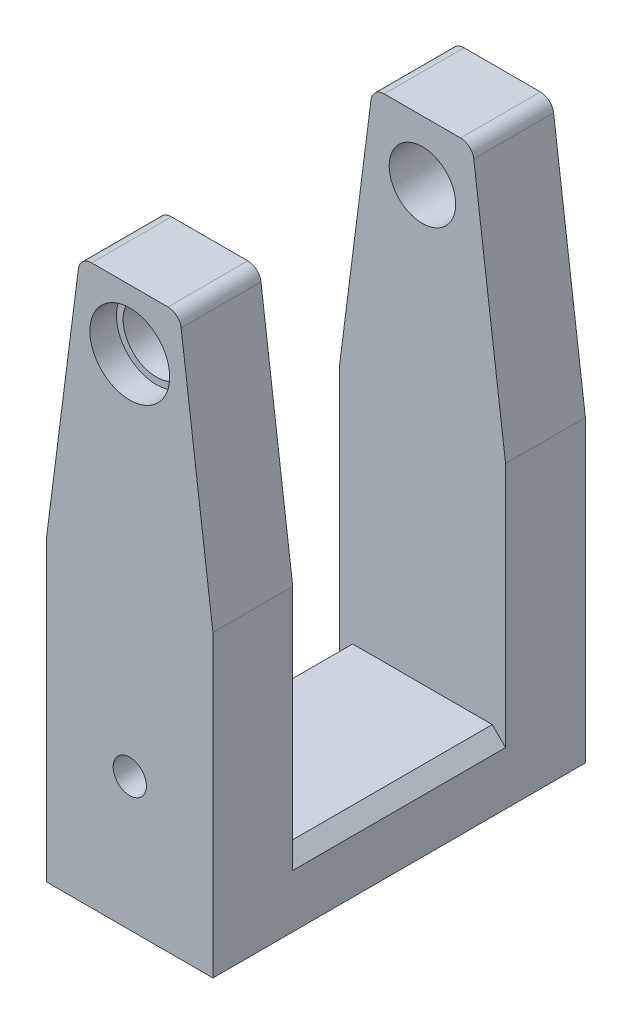
SolidWorks part; units mm, degrees
ref_plane "Front Plane" through (0, 0, 0) normal (0, 0, 1) x (1, 0, 0)
ref_plane "Top Plane" through (0, 0, 0) normal (0, 1, 0) x (1, 0, 0)
ref_plane "Right Plane" through (0, 0, 0) normal (1, 0, 0) x (0, 0, -1)
sketch "Sketch15" plane through (0, 0, 0) normal (0, 0, 1) x (1, 0, 0)
  line L6 (-12.5, 0) -> (12.5, 0)
  line L7 (0, 0) -> (0, 84) construction
  line L8 (-7.5, 84) -> (7.5, 84)
  line L9 (-12.5, 0) -> (-12.5, 45)
  line L10 (12.5, 0) -> (12.5, 45)
  line L11 (-12.5, 45) -> (-7.5, 84)
  line L12 (7.5, 84) -> (12.5, 45)
  point P4 (0, 0)
  point P9 (0, 84)
  dimension "D1" = 25
  dimension "D2" = 84
  dimension "D3" = 45
  dimension "D4" = 15
  dimension "D5" = 45
extrude "Boss-Extrude2" add sketch "Sketch15" along normal mid plane 56
sketch "Sketch16" plane through (12.5, 0, 0) normal (1, 0, 0) x (0, 0, -1)
  line L0 (-28, 84) -> (28, 84) construction
  line L1 (-16, 84) -> (16, 84)
  line L2 (-16, 84) -> (-16, 10)
  line L3 (-16, 10) -> (16, 10)
  line L4 (16, 84) -> (16, 10)
  line L5 (28, 45) -> (28, 84) construction
  line L6 (-28, 0) -> (28, 0) construction
  dimension "D1" = 12
  dimension "D2" = 32
  dimension "D3" = 10
extrude "Cut-Extrude3" cut sketch "Sketch16" against normal through all
hole_wizard "CBORE for M4 Hex Socket Head Cap Screw1" positions "Sketch17" profile "Sketch18" counterbore size "M4" standard "ISO"
sketch "Sketch17" plane through (0, 0, 28) normal (0, 0, 1) x (1, 0, 0)
  line L0 (0, 84) -> (0, 75) construction
  line L1 (7.5, 84) -> (-7.5, 84) construction
  point P0 (0, 75)
  dimension "D1" = 9
sketch "Sketch18" plane through (0, 75, 28) normal (1, 0, 0) x (0, -1, 0)
  line L0 (0, 0) -> (0, 23.0043)
  line L1 (0, 23.0043) -> (5, 20)
  line L2 (5, 20) -> (5, 4)
  line L3 (5, 4) -> (6, 4)
  line L4 (6, 4) -> (6, 0)
  line L5 (6, 0) -> (0, 0)
  line L10 (0, 23.0043) -> (-5, 20) construction
  line L11 (0, -6.35) -> (0, 107.95) construction
  dimension "Hole Dia." = 10
  dimension "Hole Depth" = 20
  dimension "C'Bore Dia." = 12
  dimension "C'Bore Depth" = 4
  dimension "Drill Angle" = 118
mirror "Mirror1" about plane through (0, 0, 0) normal (0, 0, 1) of "CBORE for M4 Hex Socket Head Cap Screw1"
hole_wizard "M6 Tapped Hole1" positions "Sketch19" profile "Sketch20" tap size "M6" standard "ISO"
sketch "Sketch19" plane through (0, 0, 28) normal (0, 0, 1) x (1, 0, 0)
  line L0 (0, 0) -> (0, 20) construction
  point P0 (0, 20)
  dimension "D1" = 20
sketch "Sketch20" plane through (0, 20, 28) normal (1, 0, 0) x (0, -1, 0)
  line L0 (0, 0) -> (0, 28.5022)
  line L1 (0, 28.5022) -> (2.5, 27)
  line L2 (2.5, 27) -> (2.5, 0)
  line L5 (2.5, 0) -> (0, 0)
  line L10 (0, 28.5022) -> (-2.5, 27) construction
  line L11 (0, -6.35) -> (0, 107.95) construction
  dimension "Tap Drill Dia." = 5
  dimension "Tap Drill Depth" = 27
  dimension "Drill Angle" = 118
cosmetic thread "Hole Thread1" parameters "D1"=12, "D2"=6
chamfer "Chamfer1" distance 2 angle 45 2 edges at (-12.5, 10, 0) (12.5, 10, 0)
fillet "Fillet1" radius 2 4 edges at (-7.5, 84, -22) (7.5, 84, -22) (-7.5, 84, 22) (7.5, 84, 22)
